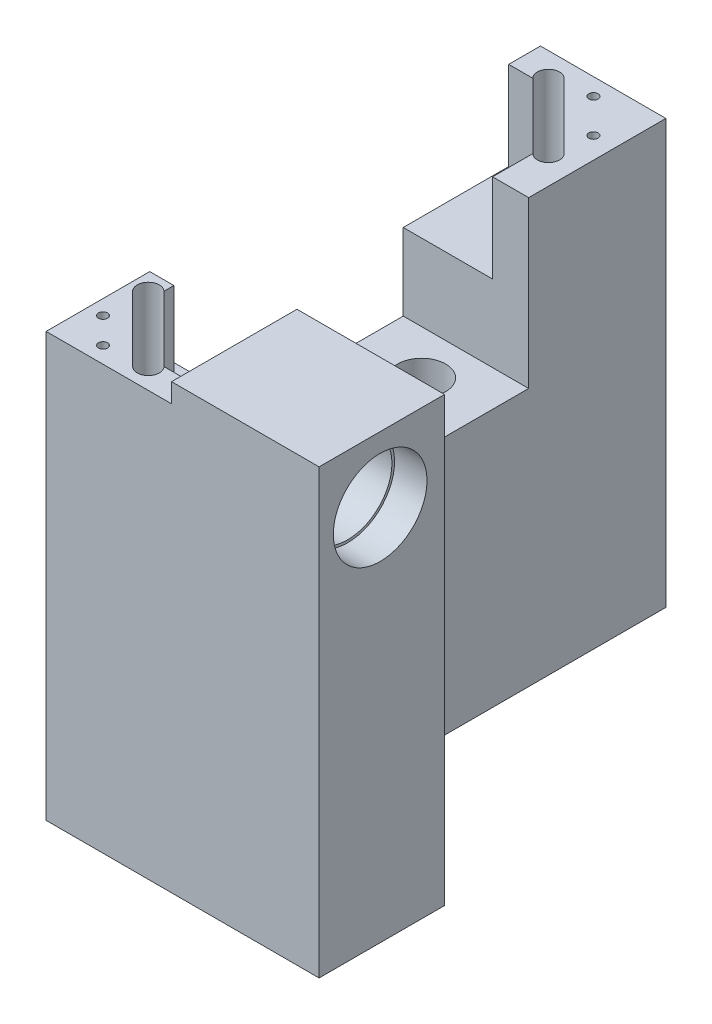
SolidWorks part; units mm, degrees
material "6061-T6 (SS)"
ref_plane "Front Plane" through (0, 0, 0) normal (0, 0, 1) x (1, 0, 0)
ref_plane "Top Plane" through (0, 0, 0) normal (0, 1, 0) x (1, 0, 0)
ref_plane "Right Plane" through (0, 0, 0) normal (1, 0, 0) x (0, 0, -1)
sketch "Sketch1" plane through (0, 0, 0) normal (0, 1, 0) x (1, 0, 0)
  line L0 (27.3648, -34.3173) -> (-9.6352, -34.3173)
  line L1 (-9.6352, -34.3173) -> (-9.6352, 32.6827)
  line L2 (-9.6352, 32.6827) -> (7.3648, 32.6827)
  line L3 (7.3648, 32.6827) -> (7.3648, -17.3173)
  line L4 (7.3648, -17.3173) -> (27.3648, -17.3173)
  line L5 (27.3648, -17.3173) -> (27.3648, -34.3173)
  dimension "D1" = 17
  dimension "D2" = 17
  dimension "D3" = 37
  dimension "D4" = 50
extrude "Boss-Extrude1" add sketch "Sketch1" along normal blind 45
sketch "Sketch2" plane through (0, 45, 0) normal (0, 1, 0) x (1, 0, 0)
  line L0 (-9.6352, 32.6827) -> (-9.6352, -34.3173) construction
  line L1 (-9.6352, 14.0846) -> (7.3648, 14.0846)
  line L2 (-9.6352, 14.0846) -> (-9.6352, -17.3173)
  line L3 (-9.6352, -17.3173) -> (7.3648, -17.3173)
  line L4 (7.3648, 14.0846) -> (7.3648, -17.3173)
  line L5 (-9.6352, 14.0846) -> (7.3648, -17.3173) construction
  line L6 (-9.6352, -17.3173) -> (7.3648, 14.0846) construction
  point P4 (-1.1352, -1.6164)
extrude "Cut-Extrude1" cut sketch "Sketch2" against normal blind 25
sketch "Sketch3" plane through (0, 0, 0) normal (0, -1, 0) x (1, 0, 0)
  line L0 (27.3648, 34.3173) -> (-9.6352, 34.3173)
  line L1 (-9.6352, 34.3173) -> (-9.6352, -32.6827)
  line L2 (-9.6352, -32.6827) -> (7.3648, -32.6827)
  line L3 (7.3648, -32.6827) -> (7.3648, 17.3173)
  line L4 (7.3648, 17.3173) -> (27.3648, 17.3173)
  line L5 (27.3648, 17.3173) -> (27.3648, 34.3173)
extrude "Boss-Extrude2" add sketch "Sketch3" along normal blind 15
sketch "Sketch4" plane through (27.3648, 0, 0) normal (1, 0, 0) x (0, 0, -1)
  circle A0 centre (-26.0434, 36.1) radius 6.35
  circle A1 centre (-26.0434, 36.1) radius 6
  dimension "D1" = 12
sketch "Sketch5" plane through (0, 45, 0) normal (0, 1, 0) x (1, 0, 0)
  line L1 (-9.6352, 32.6827) -> (7.3648, 32.6827)
  line L2 (-9.6352, 32.6827) -> (-9.6352, 14.0846)
  line L3 (-9.6352, 14.0846) -> (7.3648, 14.0846)
  line L4 (7.3648, 32.6827) -> (7.3648, 14.0846)
  line L5 (-9.6352, 32.6827) -> (7.3648, 14.0846) construction
  line L6 (-9.6352, 14.0846) -> (7.3648, 32.6827) construction
  point P4 (-1.1352, 23.3836)
extrude "Cut-Extrude2" cut sketch "Sketch5" against normal blind 2.6
sketch "Sketch6" plane through (0, 42.4, 0) normal (0, 1, 0) x (1, 0, 0)
  line L1 (-9.6352, 32.6827) -> (-9.6352, 14.0846) construction
  line L2 (-9.6352, 28.376) -> (-9.6352, 14.0846)
  line L3 (-9.6352, 14.0846) -> (2.4765, 14.0846)
  line L15 (2.4765, 19.5372) -> (2.4765, 14.0846)
  line L16 (-6.3624, 28.376) -> (-9.6352, 28.376)
  line L17 (-6.3624, 28.376) -> (2.4765, 19.5372)
extrude "Cut-Extrude3" cut sketch "Sketch6" against normal blind 12
sketch "Sketch7" plane through (0, 45, 0) normal (0, 1, 0) x (1, 0, 0)
  line L0 (2.4765, -30.4628) -> (7.3648, -30.4628)
  line L1 (7.3648, -30.4628) -> (7.3648, -17.3173)
  line L2 (7.3648, -17.3173) -> (-9.6352, -17.3173)
  line L3 (-9.6352, -17.3173) -> (-9.6352, -20.2748)
  line L4 (-9.6352, -17.3173) -> (-9.6352, -34.3173) construction
  line L8 (-8.4837, -23.7453) -> (0.3551, -32.5842)
  line L10 (-9.6352, -20.2748) -> (-6.3624, -20.2748)
  line L11 (-6.3624, -20.2748) -> (-6.3624, -21.624)
  arc A0 (-6.3624, -21.624) -> (-8.4837, -23.7453) centre (-7.423, -22.6847) ccw
  arc A1 (0.3551, -32.5842) -> (2.4765, -30.4628) centre (1.4158, -31.5235) ccw
extrude "Cut-Extrude4" cut sketch "Sketch7" against normal up to surface (14.6 mm away) up to face at (-4.136, 30.4, -20.8917)
sketch "Sketch9" plane through (27.3648, 0, 0) normal (1, 0, 0) x (0, 0, -1)
  circle A0 centre (-26.0434, 36.1) radius 6.35
extrude "Cut-Extrude6" cut sketch "Sketch4" against normal blind 4.4 contours A0
sketch "Sketch11" plane through (22.9648, 0, 0) normal (1, 0, 0) x (0, 0, -1)
  circle A0 centre (-26.0434, 36.1) radius 6
  dimension "D1" = 12
extrude "Cut-Extrude7" cut sketch "Sketch11" against normal blind 5
hole_wizard "SM05 Tapped Hole1" positions "Sketch13" profile "Sketch14" tap size "SM05" standard "UNS"
sketch "Sketch13" plane through (27.3648, 0, 0) normal (1, 0, 0) x (0, 0, -1)
  point P0 (-26.0434, 36.1)
sketch "Sketch14" plane through (27.3648, 36.1, 26.0434) normal (0, 1, 0) x (0, 0, -1)
  line L0 (0, 0) -> (0, 6.8155)
  line L1 (0, 6.8155) -> (6.35, 3)
  line L2 (6.35, 3) -> (6.35, 0)
  line L5 (6.35, 0) -> (0, 0)
  line L10 (0, 6.8155) -> (-6.35, 3) construction
  line L11 (0, -6.35) -> (0, 107.95) construction
  dimension "Tap Drill Dia." = 12.7
  dimension "Tap Drill Depth" = 3
  dimension "Drill Angle" = 118
sketch "Sketch15" plane through (0, 42.4, 0) normal (0, 1, 0) x (1, 0, 0)
  line L0 (-4.2411, 30.4973) -> (4.5978, 21.6585)
  line L1 (-6.3624, 28.376) -> (2.4765, 19.5372)
  arc A0 (-4.2411, 30.4973) -> (-6.3624, 28.376) centre (-5.3017, 29.4367) ccw
  arc A1 (2.4765, 19.5372) -> (4.5978, 21.6585) centre (3.5371, 20.5978) ccw
extrude "Cut-Extrude9" cut sketch "Sketch15" against normal blind 12.5
sketch "Sketch16" plane through (0, 30.4, 0) normal (0, 1, 0) x (1, 0, 0)
  line L0 (-6.3624, -21.624) -> (2.4765, -30.4628)
  line L2 (0.3551, -32.5842) -> (-8.4837, -23.7453)
  arc A0 (-6.3624, -21.624) -> (-8.4837, -23.7453) centre (-7.423, -22.6847) ccw
  arc A1 (2.4765, -30.4628) -> (0.3551, -32.5842) centre (1.4158, -31.5235) cw
extrude "Cut-Extrude10" cut sketch "Sketch16" against normal blind 0.5
sketch "Sketch17" plane through (0, 45, 0) normal (0, 1, 0) x (1, 0, 0)
  line L0 (7.3648, -30.4628) -> (7.3648, -34.3173)
  line L9 (-6.3624, -21.624) -> (-6.3624, -20.2748)
  line L10 (-6.3624, -20.2748) -> (-9.6352, -20.2748)
  line L11 (-9.6352, -20.2748) -> (-9.6352, -34.3173)
  line L12 (-9.6352, -34.3173) -> (27.3648, -34.3173)
  line L13 (27.3648, -34.3173) -> (27.3648, -17.3173)
  line L14 (27.3648, -17.3173) -> (7.3648, -17.3173)
  line L15 (7.3648, -17.3173) -> (7.3648, -30.4628)
  line L16 (7.3648, -30.4628) -> (2.4765, -30.4628)
  line L17 (0.3551, -32.5842) -> (-8.4837, -23.7453)
  line L18 (-6.3624, -21.624) -> (-6.3624, -20.2748)
  line L19 (-6.3624, -20.2748) -> (-9.6352, -20.2748)
  line L20 (-9.6352, -20.2748) -> (-9.6352, -34.3173)
  line L21 (-9.6352, -34.3173) -> (7.3648, -34.3173)
  line L25 (7.3648, -30.4628) -> (2.4765, -30.4628)
  line L26 (0.3551, -32.5842) -> (-8.4837, -23.7453)
  arc A2 (0.3551, -32.5842) -> (2.4765, -30.4628) centre (1.4158, -31.5235) ccw
  arc A3 (-6.3624, -21.624) -> (-8.4837, -23.7453) centre (-7.423, -22.6847) ccw
  arc A4 (0.3551, -32.5842) -> (2.4765, -30.4628) centre (1.4158, -31.5235) ccw
  arc A5 (-6.3624, -21.624) -> (-8.4837, -23.7453) centre (-7.423, -22.6847) ccw
  dimension "D1" = 0
extrude "Cut-Extrude11" cut sketch "Sketch17" against normal up to surface (2.6 mm away) up to face at (-0.6215, 42.4, -24.6644)
sketch "Sketch18" plane through (17.9648, 0, 0) normal (1, 0, 0) x (0, 0, -1)
  circle A0 centre (-26.0434, 36.1) radius 4.8998
extrude "Cut-Extrude12" cut sketch "Sketch18" against normal up to surface (10.6 mm away) up to face at (7.3648, 39.2667, 27.3658)
hole_wizard "CBORE for M3 SHCS1" positions "Sketch19" profile "Sketch20" counterbore size "M3" standard "ANSI Metric" end condition up to next
sketch "Sketch19" plane through (0, 20, 0) normal (0, 1, 0) x (1, 0, 0)
  line L0 (-9.6352, 14.0846) -> (-9.6352, -17.3173) construction
  line L1 (-9.6352, 14.0846) -> (2.4765, 14.0846) construction
  line L2 (-9.6352, -17.3173) -> (7.3648, -17.3173) construction
  point P0 (-1.1352, 8.0846)
  point P2 (-1.1352, -11.3173)
  dimension "D1" = 8.5
  dimension "D2" = 6
  dimension "D3" = 6
sketch "Sketch20" plane through (-1.1352, 20, -8.0846) normal (1, 0, 0) x (0, 0, 1)
  line L0 (0, 0) -> (0, 35)
  line L1 (0, 35) -> (1.7, 35)
  line L3 (1.7, 35) -> (1.7, 25)
  line L4 (1.7, 25) -> (3.25, 25)
  line L5 (3.25, 25) -> (3.25, 0)
  line L7 (3.25, 0) -> (0, 0)
  line L11 (0, -6.35) -> (0, 107.95) construction
  dimension "Thru Hole Dia." = 3.4
  dimension "Thru Hole Depth" = 35
  dimension "C'Bore Dia." = 6.5
  dimension "C'Bore Depth" = 25
hole_wizard "Ø3.0mm Dowel Hole1" positions "Sketch21" profile "Sketch22" hole size "Ø3.0" standard "ANSI Metric"
sketch "Sketch21" plane through (0, -15, 0) normal (0, -1, 0) x (-1, 0, 0)
  line L1 (-27.3648, -19.6934) -> (-27.3648, -32.3934) construction
  line L2 (-27.3648, -34.3173) -> (9.6352, -34.3173) construction
  line L3 (-7.3648, 32.6827) -> (-7.3648, -17.3173) construction
  line L4 (9.6352, 32.6827) -> (-7.3648, 32.6827) construction
  point P0 (-19.3648, -26.3173)
  point P1 (1.1352, 24.6827)
  dimension "D1" = 8
  dimension "D2" = 8
  dimension "D3" = 8.5
  dimension "D4" = 8
sketch "Sketch22" plane through (19.3648, -15, 26.3173) normal (1, 0, 0) x (0, 0, -1)
  line L0 (0, 0) -> (0, 6.1013)
  line L1 (0, 6.1013) -> (1.5, 5.2)
  line L2 (1.5, 5.2) -> (1.5, 0)
  line L5 (1.5, 0) -> (0, 0)
  line L10 (0, 6.1013) -> (-1.5, 5.2) construction
  line L11 (0, -6.35) -> (0, 107.95) construction
  dimension "Hole Dia." = 3
  dimension "Hole Depth" = 5.2
  dimension "Drill Angle" = 118
hole_wizard "M1.6 Tapped Hole1" positions "Sketch23" profile "Sketch24" tap size "M1.6" standard "ISO"
sketch "Sketch23" plane through (0, 42.4, 0) normal (0, 1, 0) x (1, 0, 0)
  point P0 (-0.1327, 30.3631)
  point P2 (4.4635, 25.7669)
sketch "Sketch24" plane through (-0.1327, 42.4, -30.3631) normal (1, 0, 0) x (0, 0, 1)
  line L0 (0, 0) -> (0, 4.6255)
  line L1 (0, 4.6255) -> (0.625, 4.25)
  line L2 (0.625, 4.25) -> (0.625, 0)
  line L5 (0.625, 0) -> (0, 0)
  line L10 (0, 4.6255) -> (-0.625, 4.25) construction
  line L11 (0, -6.35) -> (0, 107.95) construction
  dimension "Tap Drill Dia." = 1.25
  dimension "Tap Drill Depth" = 4.25
  dimension "Drill Angle" = 118
cosmetic thread "Hole Thread1" parameters "D1"=3.2, "D2"=1.6
cosmetic thread "Hole Thread2" parameters "D1"=3.2, "D2"=1.6
hole_wizard "M1.6 Tapped Hole2" positions "Sketch25" profile "Sketch26" tap size "M1.6" standard "ISO"
sketch "Sketch25" plane through (0, 42.4, 0) normal (0, 1, 0) x (1, 0, 0)
  point P0 (-4.1352, -32.1071)
  point P2 (-7.6352, -28.6071)
sketch "Sketch26" plane through (-4.1352, 42.4, 32.1071) normal (1, 0, 0) x (0, 0, 1)
  line L0 (0, 0) -> (0, 4.6255)
  line L1 (0, 4.6255) -> (0.625, 4.25)
  line L2 (0.625, 4.25) -> (0.625, 0)
  line L5 (0.625, 0) -> (0, 0)
  line L10 (0, 4.6255) -> (-0.625, 4.25) construction
  line L11 (0, -6.35) -> (0, 107.95) construction
  dimension "Tap Drill Dia." = 1.25
  dimension "Tap Drill Depth" = 4.25
  dimension "Drill Angle" = 118
cosmetic thread "Hole Thread3" parameters "D1"=3.2, "D2"=1.6
cosmetic thread "Hole Thread4" parameters "D1"=3.2, "D2"=1.6
